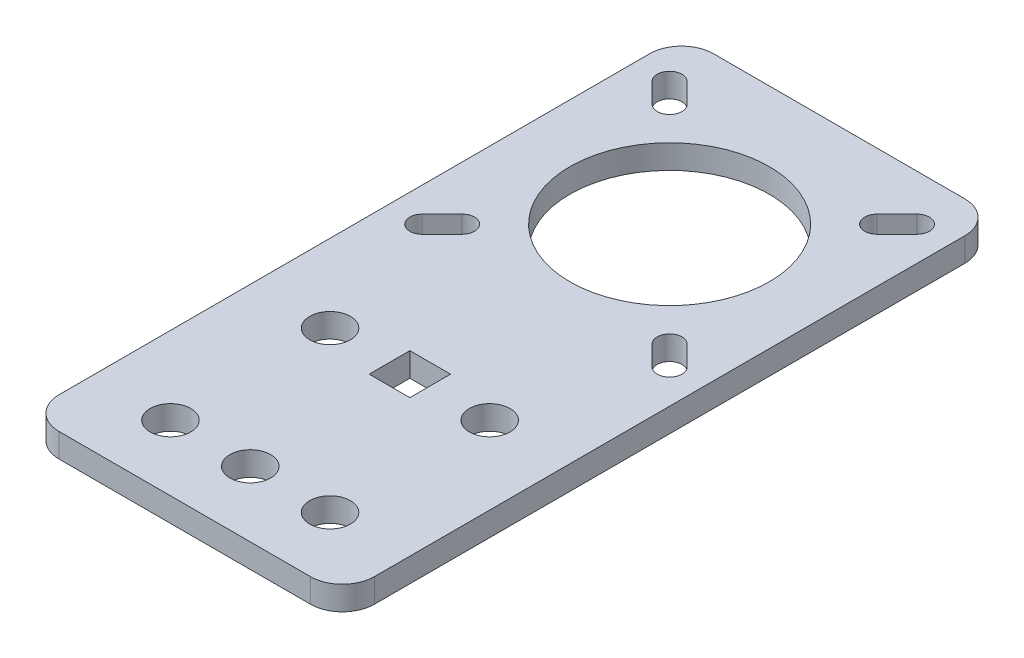
SolidWorks part; units mm, degrees
material "6061-T6 (SS)"
ref_plane "Front Plane" through (0, 0, 0) normal (0, 0, 1) x (1, 0, 0)
ref_plane "Top Plane" through (0, 0, 0) normal (0, 1, 0) x (1, 0, 0)
ref_plane "Right Plane" through (0, 0, 0) normal (1, 0, 0) x (0, 0, -1)
sketch "Sketch1" plane through (0, 0, 0) normal (0, 1, 0) x (1, 0, 0)
  line L0 (0, 0) -> (30, 0) construction
  line L1 (15.75, -60.75) -> (-15.75, -60.75)
  line L2 (19.75, -56.75) -> (19.75, 17.25)
  line L3 (15.75, 21.25) -> (-15.75, 21.25)
  line L4 (-19.75, -56.75) -> (-19.75, 17.25)
  line L5 (0, 21.25) -> (0, 0) construction
  line L6 (13, 13) -> (15.5, 15.5) construction
  line L7 (11.904, 14.096) -> (14.404, 16.596)
  line L8 (14.096, 11.904) -> (16.596, 14.404)
  line L9 (10, -52.55) -> (0, -52.55) construction
  line L10 (-13, 13) -> (-15.5, 15.5) construction
  line L11 (-11.904, 14.096) -> (-14.404, 16.596)
  line L12 (-14.096, 11.904) -> (-16.596, 14.404)
  line L13 (-13, -13) -> (-15.5, -15.5) construction
  line L14 (-11.904, -14.096) -> (-14.404, -16.596)
  line L15 (-14.096, -11.904) -> (-16.596, -14.404)
  line L16 (13, -13) -> (15.5, -15.5) construction
  line L17 (11.904, -14.096) -> (14.404, -16.596)
  line L18 (14.096, -11.904) -> (16.596, -14.404)
  line L22 (0, 0) -> (27.1737, 27.1737) construction
  arc A0 (-15.75, -60.75) -> (-19.75, -56.75) centre (-15.75, -56.75) cw
  arc A1 (15.75, -60.75) -> (19.75, -56.75) centre (15.75, -56.75) ccw
  arc A2 (19.75, 17.25) -> (15.75, 21.25) centre (15.75, 17.25) ccw
  arc A3 (-15.75, 21.25) -> (-19.75, 17.25) centre (-15.75, 17.25) ccw
  circle A4 centre (0, 0) radius 12.5
  arc A5 (11.904, 14.096) -> (14.096, 11.904) centre (13, 13) ccw
  arc A6 (16.596, 14.404) -> (14.404, 16.596) centre (15.5, 15.5) ccw
  circle A7 centre (10, -52.55) radius 2.55
  circle A8 centre (10, -32.55) radius 2.55
  circle A9 centre (0, -52.55) radius 2.55
  circle A10 centre (0, -32.55) radius 2.55
  circle A11 centre (-10, -52.55) radius 2.55
  circle A12 centre (-10, -32.55) radius 2.55
  arc A13 (-11.904, 14.096) -> (-14.096, 11.904) centre (-13, 13) cw
  arc A14 (-16.596, 14.404) -> (-14.404, 16.596) centre (-15.5, 15.5) cw
  arc A15 (-11.904, -14.096) -> (-14.096, -11.904) centre (-13, -13) ccw
  arc A16 (-16.596, -14.404) -> (-14.404, -16.596) centre (-15.5, -15.5) ccw
  arc A17 (11.904, -14.096) -> (14.096, -11.904) centre (13, -13) cw
  arc A18 (16.596, -14.404) -> (14.404, -16.596) centre (15.5, -15.5) cw
  point P4 (14.25, 14.25)
  point P40 (-14.25, 14.25)
  point P47 (-14.25, -14.25)
  point P54 (14.25, -14.25)
  dimension "D2" = 4
  dimension "D3" = 60.75
  dimension "D5" = 3.1
  dimension "D7" = 20
  dimension "D10" = 3
  dimension "D4" = 25
  dimension "D8" = 9.75
  dimension "D14" = 8.25
  dimension "D6" = 5.1
  dimension "D1" = 82
  dimension "D9" = 39.5
  dimension "D11" = 10
  dimension "D12" = 8.2
  dimension "D13" = 5.75
  dimension "D16" = 45
extrude "Boss-Extrude1" add sketch "Sketch1" along normal blind 3
sketch "Sketch2" plane through (0, 3, 0) normal (0, 1, 0) x (1, 0, 0)
  line L1 (-2.55, -35.1) -> (2.55, -35.1)
  line L2 (-2.55, -35.1) -> (-2.55, -30)
  line L3 (-2.55, -30) -> (2.55, -30)
  line L4 (2.55, -35.1) -> (2.55, -30)
  line L5 (0, -30) -> (0, -35.1) construction
  line L6 (-2.55, -32.55) -> (2.55, -32.55) construction
  circle A0 centre (0, -32.55) radius 2.55 construction
  point P0 (0, -32.55)
  point P4 (0, -30)
  point P7 (2.55, -32.55)
extrude "Cut-Extrude1" cut sketch "Sketch2" against normal through all
